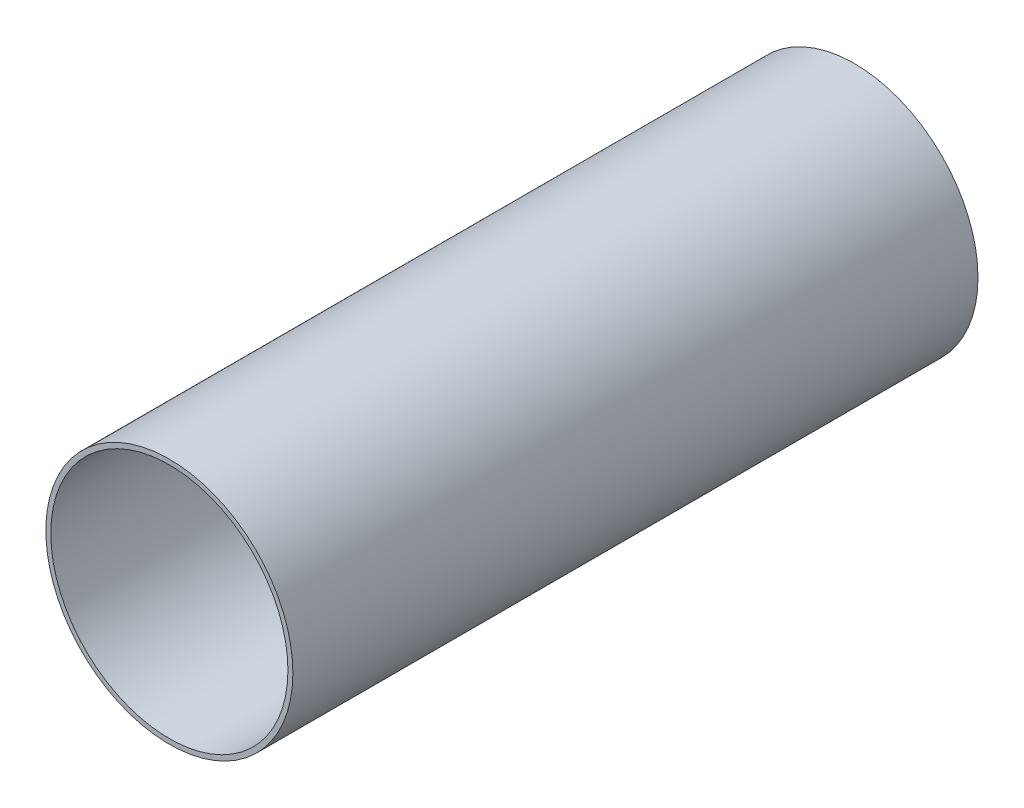
SolidWorks part; units mm, degrees
ref_plane "Front Plane" through (0, 0, 0) normal (0, 0, 1) x (1, 0, 0)
ref_plane "Top Plane" through (0, 0, 0) normal (0, 1, 0) x (1, 0, 0)
ref_plane "Right Plane" through (0, 0, 0) normal (1, 0, 0) x (0, 0, -1)
sketch "Sketch1" plane through (0, 0, 0) normal (0, 0, 1) x (1, 0, 0)
  circle A0 centre (0, 0) radius 38.1
  circle A1 centre (0, 0) radius 39.6875
  dimension "D1" = 76.2
  dimension "D2" = 1.5875
extrude "Boss-Extrude1" add sketch "Sketch1" along normal blind 220.1418
